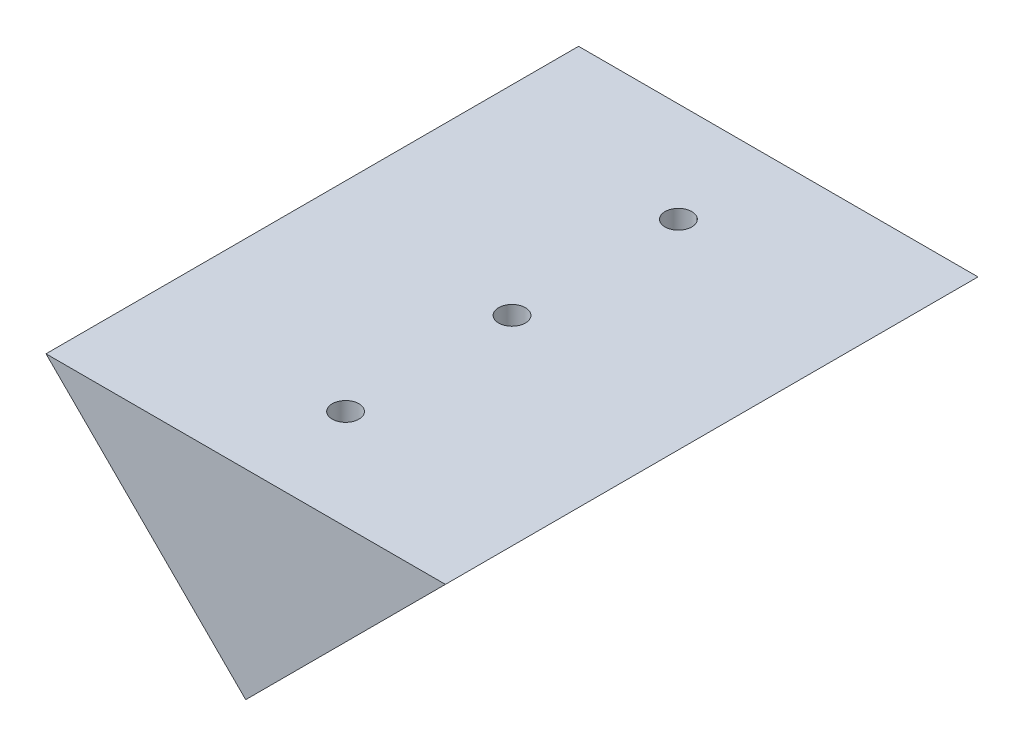
SolidWorks part; units mm, degrees
material "Pine"
ref_plane "Front Plane" through (0, 0, 0) normal (0, 0, 1) x (1, 0, 0)
ref_plane "Top Plane" through (0, 0, 0) normal (0, 1, 0) x (1, 0, 0)
ref_plane "Right Plane" through (0, 0, 0) normal (1, 0, 0) x (0, 0, -1)
sketch "Sketch2" plane through (0, 0, 0) normal (0, 0, 1) x (1, 0, 0)
  line L0 (-91.4692, 25.4) -> (-53.3692, -12.7)
  line L1 (-53.3692, 25.4) -> (-53.3692, -12.7) construction
  line L3 (-91.4692, 25.4) -> (-15.2692, 25.4)
  line L7 (-53.3692, -12.7) -> (-15.2692, 25.4)
  point P0 (0, 0)
  dimension "D1" = 76.2
  dimension "D2" = 38.1
extrude "Main extrude" add sketch "Sketch2" along normal blind 101.6
hole_wizard "Mounting holes" positions "Sketch4" profile "Sketch3" tap size "1/4-20" standard "ANSI Inch"
sketch "Sketch4" plane through (0, 25.4, 0) normal (0, 1, 0) x (1, 0, 0)
  line L0 (-53.3692, 0) -> (-53.3692, -101.6) construction
  line L1 (-15.2692, 0) -> (-91.4692, 0) construction
  line L2 (-15.2692, -101.6) -> (-91.4692, -101.6) construction
  line L4 (-15.2692, -50.8) -> (-91.4692, -50.8) construction
  line L5 (-15.2692, -101.6) -> (-15.2692, 0) construction
  line L6 (-91.4692, -101.6) -> (-91.4692, 0) construction
  point P17 (-53.3692, -19.05)
  point P19 (-53.3692, -82.55)
  point P22 (-53.3692, -50.8)
  dimension "D1" = 63.5
sketch "Sketch3" plane through (-53.3692, 25.4, 19.05) normal (1, 0, 0) x (0, 0, 1)
  line L0 (0, 0) -> (0, 18.0438)
  line L1 (0, 18.0438) -> (2.5527, 16.51)
  line L2 (2.5527, 16.51) -> (2.5527, 0)
  line L5 (2.5527, 0) -> (0, 0)
  line L10 (0, 18.0438) -> (-2.5527, 16.51) construction
  line L11 (0, -6.35) -> (0, 107.95) construction
  dimension "Tap Drill Dia." = 5.1054
  dimension "Tap Drill Depth" = 16.51
  dimension "Drill Angle" = 118
cosmetic thread "Hole Thread1"
cosmetic thread "Hole Thread2"
cosmetic thread "Hole Thread3"
hole_wizard "Bearing mount left" positions "Sketch6" profile "Sketch5" tap size "1/4-20" standard "ANSI Inch"
sketch "Sketch6" plane through (-20.3346, 20.3346, 0) normal (0.7071, -0.7071, 0) x (-0.7071, -0.7071, 0)
  line L0 (21.318, 0) -> (21.318, -101.6) construction
  line L1 (46.718, 0) -> (-7.1635, 0) construction
  line L2 (46.718, -101.6) -> (-7.1635, -101.6) construction
  line L4 (46.718, -101.6) -> (46.718, 0) construction
  line L5 (-7.1635, -50.8) -> (46.718, -50.8) construction
  line L6 (-7.1635, -101.6) -> (-7.1635, 0) construction
  point P16 (21.318, -12.7)
  point P18 (21.318, -88.9)
  dimension "D1" = 25.4
  dimension "D2" = 76.2
sketch "Sketch5" plane through (-35.4087, 5.2605, 12.7) normal (0, 0, 1) x (0.7071, 0.7071, 0)
  line L0 (0, 0) -> (0, 14.2338)
  line L1 (0, 14.2338) -> (2.5527, 12.7)
  line L2 (2.5527, 12.7) -> (2.5527, 0)
  line L5 (2.5527, 0) -> (0, 0)
  line L10 (0, 14.2338) -> (-2.5527, 12.7) construction
  line L11 (0, -6.35) -> (0, 107.95) construction
  dimension "Tap Drill Dia." = 5.1054
  dimension "Tap Drill Depth" = 12.7
  dimension "Drill Angle" = 118
cosmetic thread "Hole Thread4"
cosmetic thread "Hole Thread5"
hole_wizard "Bearing mount right" positions "Sketch8" profile "Sketch7" tap size "1/4-20" standard "ANSI Inch"
sketch "Sketch8" plane through (-33.0346, -33.0346, 0) normal (-0.7071, -0.7071, 0) x (-0.7071, 0.7071, 0)
  line L0 (54.1575, 0) -> (54.1575, -101.6) construction
  line L1 (82.639, 0) -> (28.7575, 0) construction
  line L2 (82.639, -101.6) -> (28.7575, -101.6) construction
  line L4 (82.639, -50.8) -> (28.7575, -50.8) construction
  line L5 (82.639, -101.6) -> (82.639, 0) construction
  line L6 (28.7575, -101.6) -> (28.7575, 0) construction
  point P17 (54.1575, -82.55)
  point P19 (54.1575, -19.05)
  dimension "D1" = 63.5
  dimension "D2" = 25.4
sketch "Sketch7" plane through (-71.3297, 5.2605, 82.55) normal (0, 0, 1) x (0.7071, -0.7071, 0)
  line L0 (0, 0) -> (0, 18.0438)
  line L1 (0, 18.0438) -> (2.5527, 16.51)
  line L2 (2.5527, 16.51) -> (2.5527, 0)
  line L5 (2.5527, 0) -> (0, 0)
  line L10 (0, 18.0438) -> (-2.5527, 16.51) construction
  line L11 (0, -6.35) -> (0, 107.95) construction
  dimension "Tap Drill Dia." = 5.1054
  dimension "Tap Drill Depth" = 16.51
  dimension "Drill Angle" = 118
cosmetic thread "Hole Thread6"
cosmetic thread "Hole Thread7"
